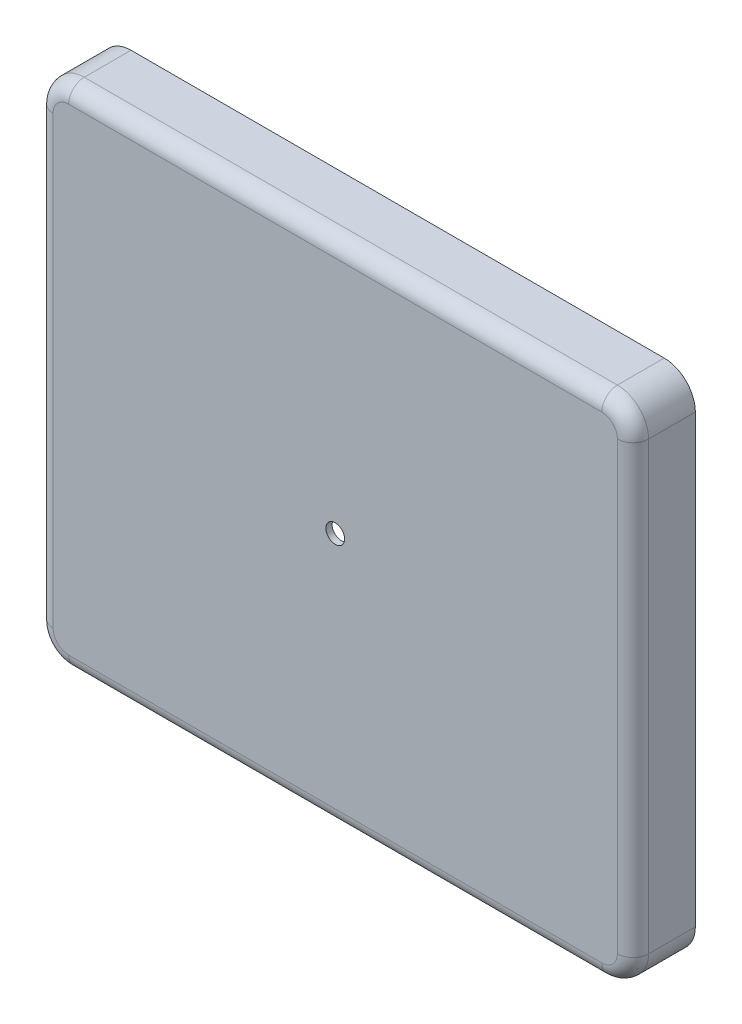
SolidWorks part; units mm, degrees
ref_plane "Front Plane" through (0, 0, 0) normal (0, 0, 1) x (1, 0, 0)
ref_plane "Top Plane" through (0, 0, 0) normal (0, 1, 0) x (1, 0, 0)
ref_plane "Right Plane" through (0, 0, 0) normal (1, 0, 0) x (0, 0, -1)
sketch "Sketch1" plane through (0, 0, 0) normal (0, 0, 1) x (1, 0, 0)
  line L1 (-95.5, 81.5) -> (95.5, 81.5)
  line L2 (-95.5, 81.5) -> (-95.5, -81.5)
  line L3 (-95.5, -81.5) -> (95.5, -81.5)
  line L4 (95.5, 81.5) -> (95.5, -81.5)
  line L5 (-95.5, 81.5) -> (95.5, -81.5) construction
  line L6 (-95.5, -81.5) -> (95.5, 81.5) construction
  point P0 (0, 0)
  dimension "D1" = 191
  dimension "D2" = 163
extrude "Boss-Extrude1" add sketch "Sketch1" along normal blind 20
fillet "Fillet1" radius 10 4 edges at (-95.5, -81.5, 10) (95.5, -81.5, 10) (95.5, 81.5, 10) (-95.5, 81.5, 10)
fillet "Fillet2" radius 5 8 edges at (-92.5711, 78.5711, 20) (0, 81.5, 20) (92.5711, 78.5711, 20) (95.5, 0, 20) (92.5711, -78.5711, 20) (0, -81.5, 20) (-92.5711, -78.5711, 20) (-95.5, 0, 20)
shell "Shell1" thickness 2
sketch "Sketch2" plane through (0, 0, 18) normal (0, 0, -1) x (-1, 0, 0)
  circle A0 centre (0, 0) radius 3
  dimension "D1" = 6
extrude "Cut-Extrude1" cut sketch "Sketch2" against normal blind 10
